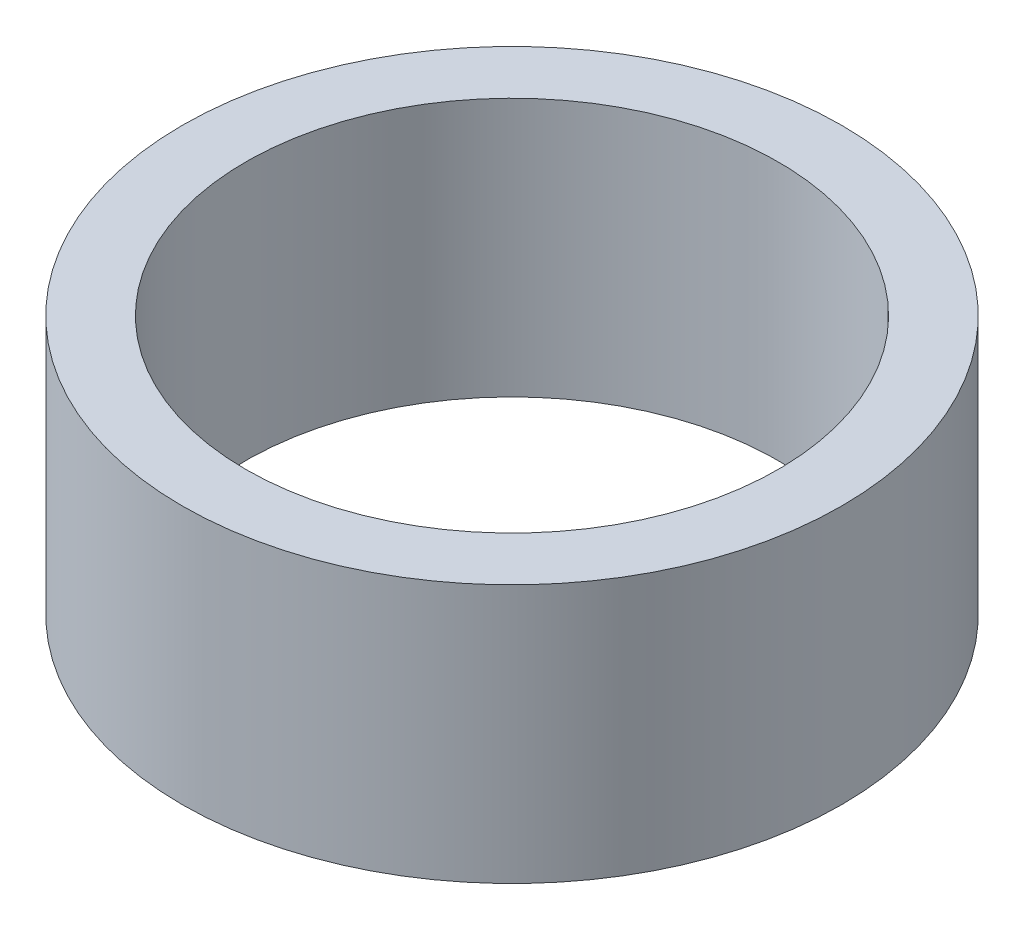
SolidWorks part; units mm, degrees
ref_plane "Front Plane" through (0, 0, 0) normal (0, 0, 1) x (1, 0, 0)
ref_plane "Top Plane" through (0, 0, 0) normal (0, 1, 0) x (1, 0, 0)
ref_plane "Right Plane" through (0, 0, 0) normal (1, 0, 0) x (0, 0, -1)
sketch "Sketch1" plane through (0, 0, 0) normal (0, 1, 0) x (1, 0, 0)
  circle A0 centre (0, 0) radius 65
  circle A1 centre (0, 0) radius 52.5
  dimension "D1" = 130
  dimension "D2" = 105
extrude "Boss-Extrude1" add sketch "Sketch1" along normal blind 51
